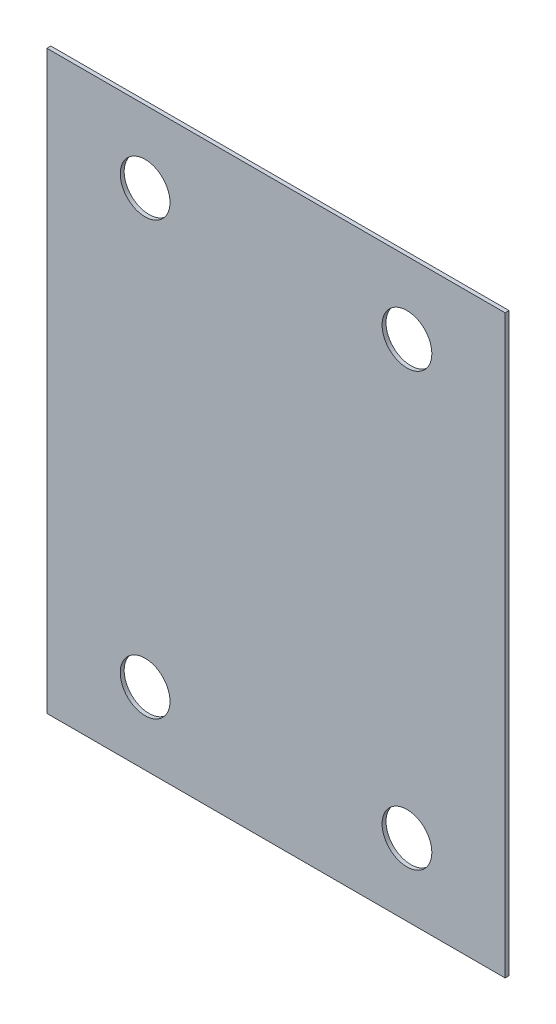
SolidWorks part; units mm, degrees
ref_plane "Спереди" through (0, 0, 0) normal (0, 0, 1) x (1, 0, 0)
ref_plane "Сверху" through (0, 0, 0) normal (0, 1, 0) x (1, 0, 0)
ref_plane "Справа" through (0, 0, 0) normal (1, 0, 0) x (0, 0, -1)
sketch "Эскиз1" plane through (0, 0, 0) normal (0, 0, 1) x (1, 0, 0)
  line L0 (175, -220) -> (175, 220)
  line L1 (175, 220) -> (-175, 220)
  line L2 (-175, 220) -> (-175, -220)
  line L3 (-175, -220) -> (175, -220)
  circle A4 centre (-100, 165) radius 19
  circle A5 centre (100, 165) radius 19
  circle A6 centre (100, -165) radius 19
  circle A7 centre (-100, -165) radius 19
extrude "Бобышка-Вытянуть1" add sketch "Эскиз1" along normal blind 3
